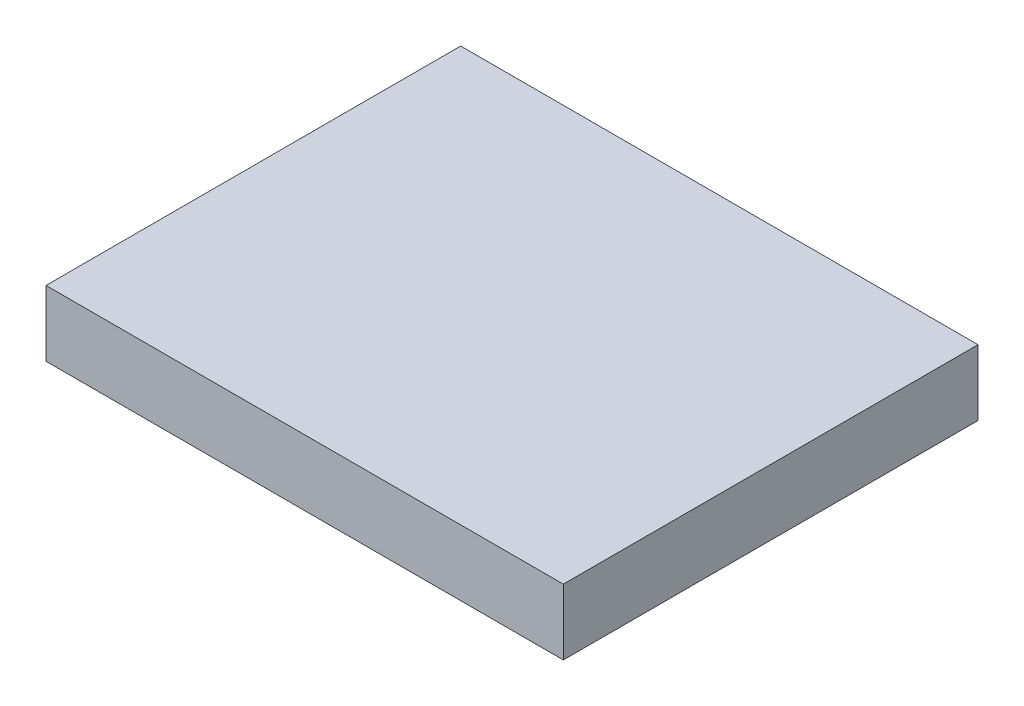
SolidWorks part; units mm, degrees
ref_plane "Front Plane" through (0, 0, 0) normal (0, 0, 1) x (1, 0, 0)
ref_plane "Top Plane" through (0, 0, 0) normal (0, 1, 0) x (1, 0, 0)
ref_plane "Right Plane" through (0, 0, 0) normal (1, 0, 0) x (0, 0, -1)
sketch "Sketch1" plane through (0, 0, 0) normal (0, 1, 0) x (1, 0, 0)
  line L1 (-31.5, -25.25) -> (31.5, -25.25)
  line L2 (-31.5, -25.25) -> (-31.5, 25.25)
  line L3 (-31.5, 25.25) -> (31.5, 25.25)
  line L4 (31.5, -25.25) -> (31.5, 25.25)
  line L5 (-31.5, -25.25) -> (31.5, 25.25) construction
  line L6 (-31.5, 25.25) -> (31.5, -25.25) construction
  point P0 (0, 0)
  dimension "D1" = 63
  dimension "D2" = 50.5
extrude "Boss-Extrude1" add sketch "Sketch1" along normal blind 8
